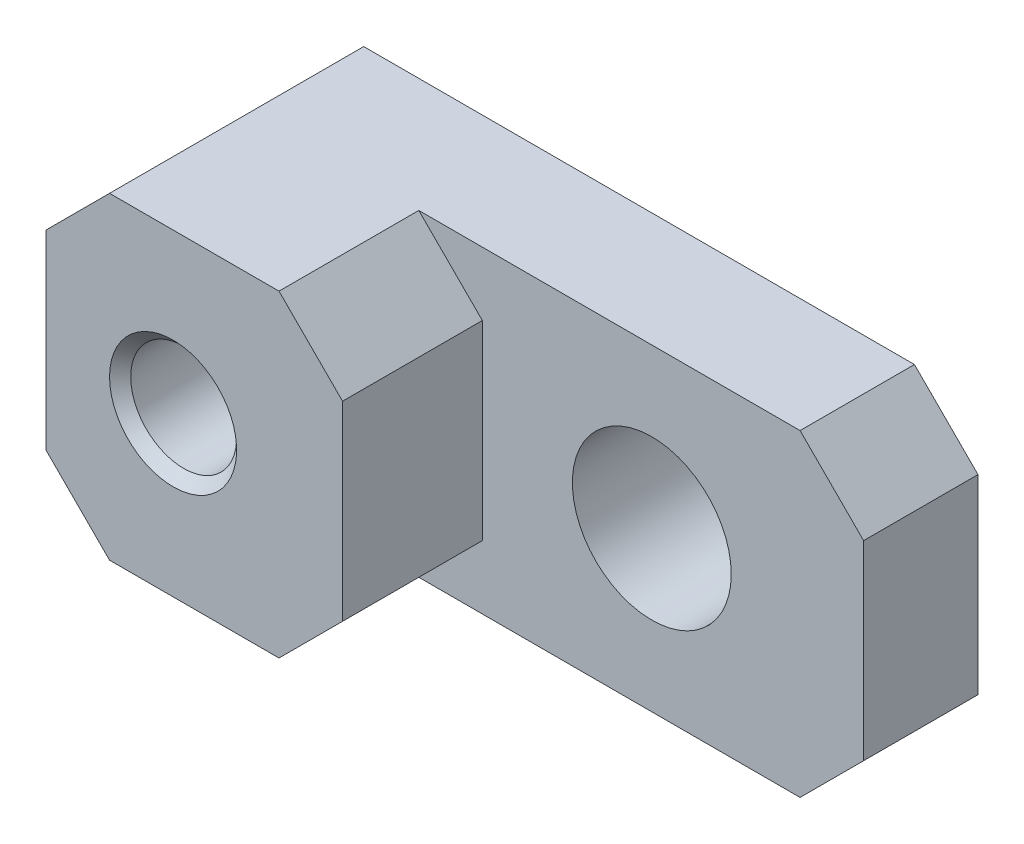
SolidWorks part; units mm, degrees
material "6061-T6 Al"
ref_plane "Front" through (0, 0, 0) normal (0, 0, 1) x (1, 0, 0)
ref_plane "Top" through (0, 0, 0) normal (0, 1, 0) x (1, 0, 0)
ref_plane "Right" through (0, 0, 0) normal (1, 0, 0) x (0, 0, -1)
sketch "Sketch1" plane through (0, 0, 0) normal (0, 0, 1) x (1, 0, 0)
  line L0 (0, 4.7625) -> (20.32, 4.7625) construction
  line L1 (0, 0) -> (20.32, 0)
  line L2 (0, 0) -> (0, 9.525)
  line L3 (0, 9.525) -> (20.32, 9.525)
  line L4 (20.32, 0) -> (20.32, 9.525)
  dimension "D1" = 20.32
  dimension "D2" = 9.525
extrude "Extrude1" add sketch "Sketch1" along normal blind 7.62
hole_wizard "3/16 (0.1875) Diameter Hole1" positions "Sketch3" profile "Sketch2" hole size "3/16" standard "Ansi Inch" end condition through all
sketch "Sketch3" plane through (4.0423, -0.4952, 7.62) normal (0, 0, -1) x (-1, 0, 0)
  line L0 (4.0423, 5.2577) -> (-9.9277, 5.2577) construction
  line L1 (4.0423, 10.0202) -> (4.0423, 0.4952) construction
  point P0 (-9.9277, 5.2577)
  dimension "D1" = 13.97
sketch "Sketch2" plane through (13.97, 4.7625, 7.62) normal (1, 0, 0) x (0, -1, 0)
  line L0 (0, 0) -> (0, 7.62)
  line L1 (0, 7.62) -> (2.3812, 7.62)
  line L2 (2.3812, 7.62) -> (2.3812, 0)
  line L5 (2.3812, 0) -> (0, 0)
  line L11 (0, -6.35) -> (0, 107.95) construction
  dimension "Thru Hole Dia." = 4.7625
  dimension "Thru Hole Depth" = 7.62
sketch "Sketch4" plane through (0, 0, 7.62) normal (0, 0, 1) x (1, 0, 0)
  line L0 (8.89, 9.525) -> (8.89, 0)
  line L1 (0, 9.525) -> (0, 0) construction
  line L4 (0, 9.525) -> (0, 0)
  line L5 (0, 0) -> (20.32, 0)
  line L6 (20.32, 0) -> (20.32, 9.525)
  line L7 (20.32, 9.525) -> (0, 9.525)
  line L9 (8.89, 0) -> (20.32, 0)
  line L10 (20.32, 0) -> (20.32, 9.525)
  line L11 (20.32, 9.525) -> (8.89, 9.525)
  dimension "D2" = 8.89
  dimension "D1" = 0
extrude "Extrude2" cut sketch "Sketch4" against normal blind 4.191
chamfer "Chamfer1" distance 1.905 angle 45 8 edges at (0, 4.7625, 0) (0, 4.7625, 7.62) (8.89, 0, 5.5245) (8.89, 9.525, 5.5245) (20.32, 9.525, 1.7145) (20.32, 0, 1.7145) (0, 9.525, 3.81) (0, 0, 3.81)
hole_wizard "CBORE for #4 Socket Head Cap Screw1" positions "Sketch6" profile "Sketch5" counterbore size "#4" standard "Ansi Inch" end condition through all
sketch "Sketch6" plane through (0, 0, 0) normal (0, 0, -1) x (-1, 0, 0)
  line L0 (-13.97, 4.7625) -> (-3.81, 4.7625) construction
  point P0 (-3.81, 4.7625)
  dimension "D1" = 10.16
sketch "Sketch5" plane through (3.81, 4.7625, 0) normal (1, 0, 0) x (0, 1, 0)
  line L0 (0, 0) -> (0, 7.62)
  line L1 (1.5875, 7.3025) -> (1.905, 7.62)
  line L2 (1.6002, 1.524) -> (1.5875, 1.524)
  line L3 (1.5875, 1.524) -> (1.5875, 7.3025)
  line L5 (1.6002, 1.524) -> (1.6002, 0.3048)
  line L6 (1.6002, 0.3048) -> (1.905, 0)
  line L7 (1.905, 0) -> (0, 0)
  line L8 (-1.6002, 0.3048) -> (-1.905, 0) construction
  line L11 (0, -6.35) -> (0, 107.95) construction
  line L12 (1.905, 7.62) -> (0, 7.62)
  line L13 (-1.5875, 7.3025) -> (-1.905, 7.62) construction
  dimension "Thru Hole Dia." = 3.175
  dimension "Thru Hole Depth" = 7.62
  dimension "C'Bore Dia." = 3.2004
  dimension "C'Bore Depth" = 1.524
  dimension "Near C'Sink Dia." = 3.81
  dimension "Near C'Sink Angle" = 90
  dimension "Far C'Sink Dia." = 3.81
  dimension "Far C'Sink Angle" = 90
